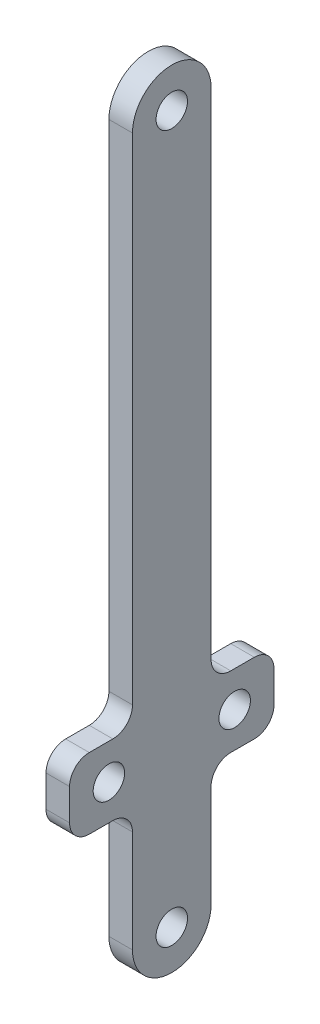
SolidWorks part; units mm, degrees
ref_plane "Front Plane" through (0, 0, 0) normal (0, 0, 1) x (1, 0, 0)
ref_plane "Top Plane" through (0, 0, 0) normal (0, 1, 0) x (1, 0, 0)
ref_plane "Right Plane" through (0, 0, 0) normal (1, 0, 0) x (0, 0, -1)
sketch "Sketch2" plane through (0, 0, 0) normal (1, 0, 0) x (0, 0, -1)
  line L0 (0, 0) -> (0, 180) construction
  line L1 (-10, 0) -> (-10, 180)
  line L2 (10, 0) -> (10, 180)
  line L3 (-26, 40) -> (26, 40) construction
  line L4 (-26, 31) -> (26, 31)
  line L5 (-26, 31) -> (-26, 49)
  line L6 (-26, 49) -> (26, 49)
  line L7 (26, 31) -> (26, 49)
  line L8 (-26, 31) -> (26, 49) construction
  line L9 (-26, 49) -> (26, 31) construction
  line L10 (-16, 40) -> (-16, 31) construction
  line L11 (0, 0) -> (0, -48.0135) construction
  arc A0 (-10, 0) -> (10, 0) centre (0, 0) ccw
  arc A1 (10, 180) -> (-10, 180) centre (0, 180) ccw
  circle A2 centre (0, 0) radius 4
  circle A3 centre (-16, 40) radius 4
  circle A4 centre (-16, 40) radius 16 construction
  circle A5 centre (16, 40) radius 4
  circle A6 centre (0, 180) radius 4
  point P3 (0, 90)
  dimension "D2" = 8
  dimension "D3" = 10
  dimension "D4" = 140
  dimension "D6" = 8
  dimension "D7" = 32
  dimension "D9" = 8
  dimension "D1" = 40
  dimension "D5" = 18
  dimension "D8" = 10
extrude "Boss-Extrude1" add sketch "Sketch2" along normal blind 6 contours L6 L5 L4 L1 A3 | L6 L1 L4 L2 | L4 L7 L6 L2 | L2 A1 L1 L6 | L1 A0 L2 L4 A2
fillet "Fillet1" radius 5 8 edges at (3, 49, -10) (3, 49, -26) (3, 31, -26) (3, 31, -10) (3, 31, 10) (3, 31, 26) (3, 49, 26) (3, 49, 10)
